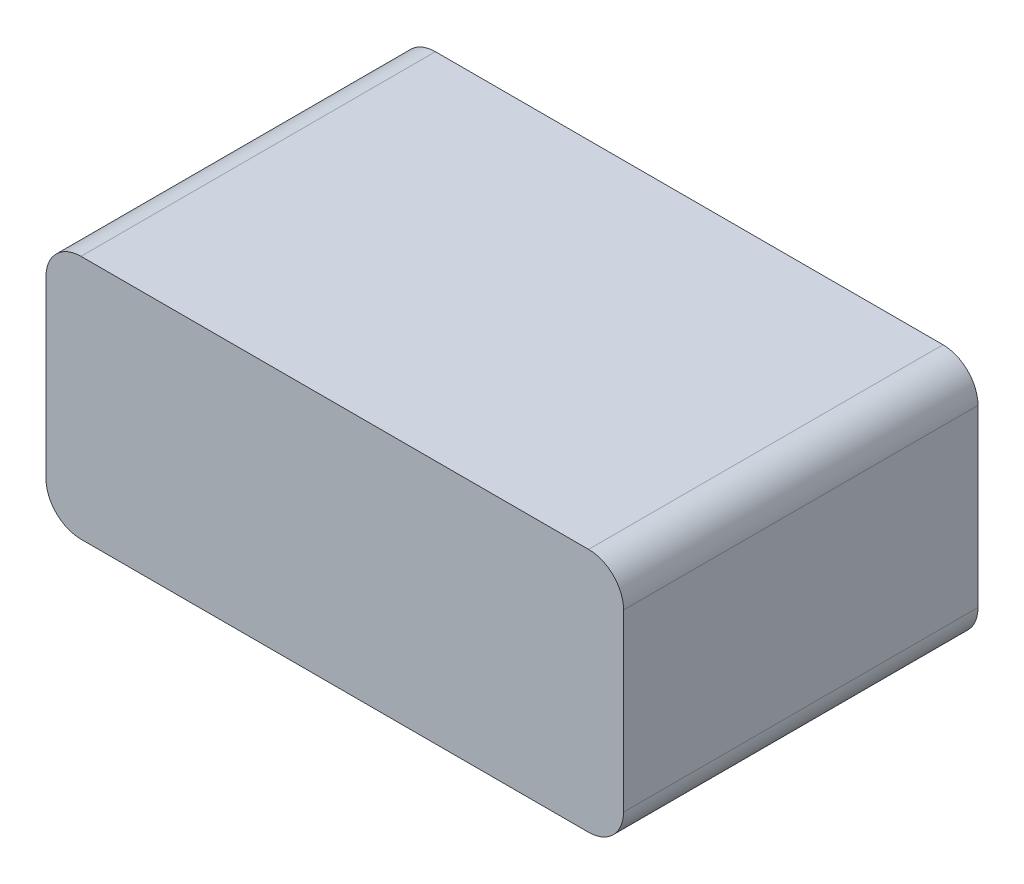
SolidWorks part; units mm, degrees
ref_plane "Front Plane" through (0, 0, 0) normal (0, 0, 1) x (1, 0, 0)
ref_plane "Top Plane" through (0, 0, 0) normal (0, 1, 0) x (1, 0, 0)
ref_plane "Right Plane" through (0, 0, 0) normal (1, 0, 0) x (0, 0, -1)
sketch "Sketch1" plane through (0, 0, 0) normal (0, 1, 0) x (1, 0, 0)
  line L5 (-25.1978, 92.3087) -> (184.3522, 92.3087)
  line L6 (-25.1978, 92.3087) -> (-25.1978, -36.2788)
  line L7 (-25.1978, -36.2788) -> (184.3522, -36.2788)
  line L8 (184.3522, 92.3087) -> (184.3522, -36.2788)
extrude "Boss-Extrude1" add sketch "Sketch1" along normal blind 88.9
fillet "Fillet1" radius 12.7 1 edges at (184.3522, 88.9, -28.0149)
fillet "Fillet2" radius 12.7 1 edges at (-25.1978, 88.9, -28.0149)
fillet "Fillet3" radius 12.7 1 edges at (-25.1978, 0, -28.0149)
fillet "Fillet4" radius 12.7 1 edges at (184.3522, 0, -28.0149)
shell "Shell1" thickness 2.54
